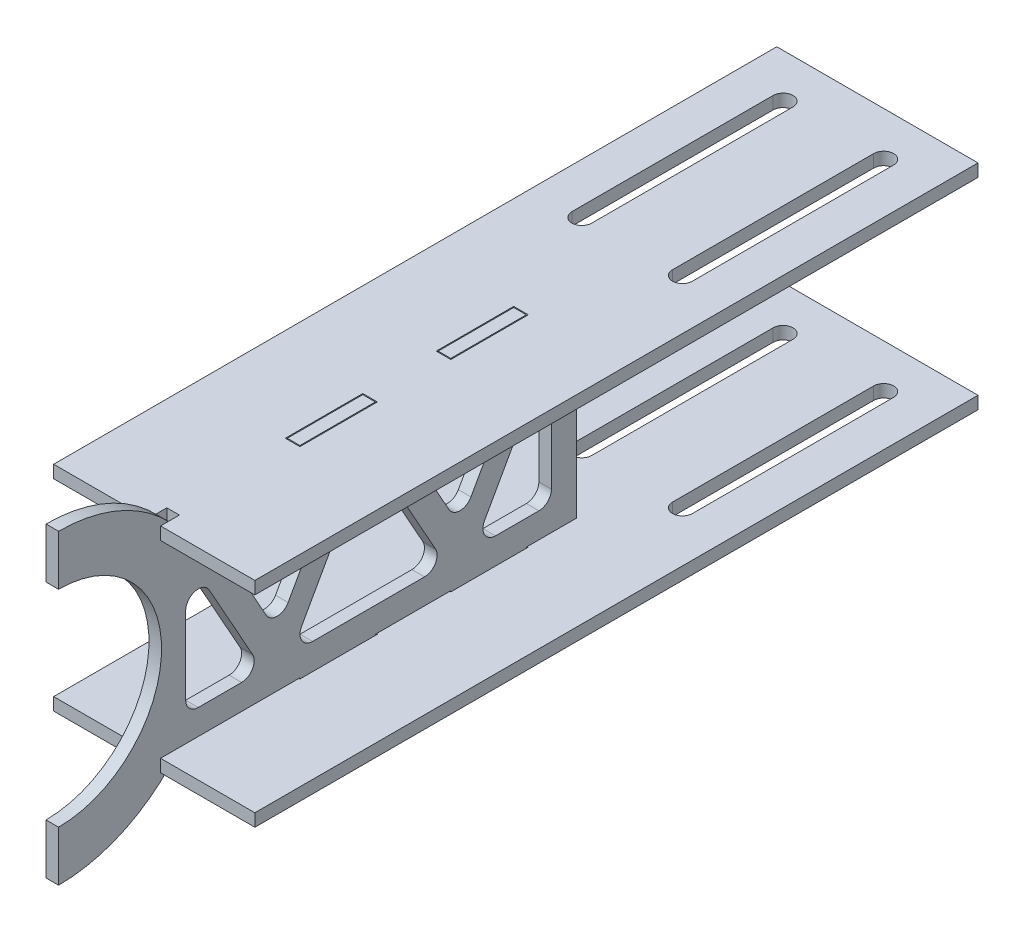
SolidWorks part; units mm, degrees
material "AISI 1020"
ref_plane "Front Plane" through (0, 0, 0) normal (0, 0, 1) x (1, 0, 0)
ref_plane "Top Plane" through (0, 0, 0) normal (0, 1, 0) x (1, 0, 0)
ref_plane "Right Plane" through (0, 0, 0) normal (1, 0, 0) x (0, 0, -1)
sketch "Sketch1" plane through (0, 0, 0) normal (1, 0, 0) x (0, 0, -1)
  line L0 (0, 0) -> (160.9375, 0) construction
  line L1 (30.5066, 23.8125) -> (60.925, 23.8125)
  line L2 (30.5066, -23.8125) -> (60.925, -23.8125)
  line L3 (130.775, 23.8125) -> (130.775, -23.8125)
  line L4 (0, 38.7) -> (0, 26)
  line L5 (137.125, 23.8125) -> (184.75, 23.8125) construction
  line L6 (137.125, 23.8125) -> (137.125, -23.8125) construction
  line L7 (137.125, -23.8125) -> (184.75, -23.8125) construction
  line L8 (184.75, 23.8125) -> (184.75, -23.8125) construction
  line L9 (137.125, 23.8125) -> (184.75, -23.8125) construction
  line L10 (137.125, -23.8125) -> (184.75, 23.8125) construction
  line L11 (0, -26) -> (0, -38.7)
  line L34 (60.925, 23.8125) -> (60.925, 26.9875)
  line L35 (60.925, 26.9875) -> (79.975, 26.9875)
  line L36 (79.975, 26.9875) -> (79.975, 23.8125)
  line L37 (99.025, 23.8125) -> (99.025, 26.9875)
  line L38 (99.025, 26.9875) -> (118.075, 26.9875)
  line L39 (118.075, 26.9875) -> (118.075, 23.8125)
  line L40 (118.075, 23.8125) -> (130.775, 23.8125)
  line L41 (79.975, 23.8125) -> (99.025, 23.8125)
  line L43 (79.975, -23.8125) -> (99.025, -23.8125)
  line L44 (118.075, -26.9875) -> (118.075, -23.8125)
  line L45 (99.025, -26.9875) -> (118.075, -26.9875)
  line L46 (99.025, -23.8125) -> (99.025, -26.9875)
  line L47 (79.975, -26.9875) -> (79.975, -23.8125)
  line L48 (60.925, -26.9875) -> (79.975, -26.9875)
  line L49 (60.925, -23.8125) -> (60.925, -26.9875)
  line L52 (118.075, -23.8125) -> (130.775, -23.8125)
  arc A0 (0, -26) -> (0, 26) centre (0, 0) ccw
  arc A1 (30.5066, 23.8125) -> (0, 38.7) centre (0, 0) ccw
  arc A2 (0, -38.7) -> (30.5066, -23.8125) centre (0, 0) ccw
  circle A6 centre (0, 0) radius 48.225 construction
  point P1 (48.225, 0)
  point P11 (130.775, 0)
  dimension "D1" = 52
  dimension "D6" = 12.7
  dimension "D7" = 12.7
  dimension "D10" = 9.525
  dimension "D2" = 12.7
  dimension "D3" = 47.625
  dimension "D4" = 47.625
  dimension "D5" = 6.35
  dimension "D17" = 19.05
  dimension "D18" = 3.175
  dimension "D19" = 19.05
extrude "Boss-Extrude1" add sketch "Sketch1" along normal mid plane 3.175
sketch "Sketch2" plane through (0, 23.8125, 0) normal (0, 1, 0) x (1, 0, 0)
  line L0 (-1.5875, 30.5066) -> (1.5875, 30.5066)
  line L1 (1.5875, 30.5066) -> (-1.5875, 30.5066) construction
  line L2 (1.5875, 30.5066) -> (1.5875, 25.7441)
  line L3 (1.5875, 25.7441) -> (25.4, 25.7441)
  line L4 (25.4, 25.7441) -> (25.4, 208.3066)
  line L5 (25.4, 208.3066) -> (-25.4, 208.3066)
  line L6 (0, 208.3066) -> (0, 30.5066) construction
  line L7 (-12.7, 197.1941) -> (-12.7, 146.3941) construction
  line L8 (-12.7, 159.0941) -> (12.7, 159.0941) construction
  line L9 (-12.7, 159.0941) -> (-12.7, 184.4941) construction
  line L10 (-12.7, 184.4941) -> (12.7, 184.4941) construction
  line L12 (-12.7, 159.0941) -> (12.7, 184.4941) construction
  line L13 (-12.7, 184.4941) -> (12.7, 159.0941) construction
  line L14 (-12.7, 171.7941) -> (0, 171.7941) construction
  line L17 (12.7, 146.3941) -> (12.7, 197.1941) construction
  line L20 (10.1917, 146.3941) -> (10.1917, 197.1941)
  line L23 (15.2083, 146.3941) -> (15.2083, 197.1941)
  line L26 (-1.5875, 30.5066) -> (-1.5875, 25.7441)
  line L27 (-1.5875, 25.7441) -> (-25.4, 25.7441)
  line L28 (-25.4, 25.7441) -> (-25.4, 208.3066)
  line L29 (-1.5875, 118.075) -> (-1.5875, 99.025) construction
  line L30 (-1.5875, 99.025) -> (1.5875, 99.025) construction
  line L31 (1.5875, 99.025) -> (1.5875, 118.075) construction
  line L32 (1.5875, 118.075) -> (-1.5875, 118.075) construction
  line L33 (-1.5875, 79.975) -> (-1.5875, 60.925) construction
  line L34 (-1.5875, 60.925) -> (1.5875, 60.925) construction
  line L35 (1.5875, 60.925) -> (1.5875, 79.975) construction
  line L36 (1.5875, 79.975) -> (-1.5875, 79.975) construction
  line L37 (-1.5875, 118.075) -> (-1.5875, 99.025) construction
  line L38 (-1.5875, 99.025) -> (1.5875, 99.025) construction
  line L39 (1.5875, 99.025) -> (1.5875, 118.075) construction
  line L40 (1.5875, 118.075) -> (-1.5875, 118.075) construction
  line L41 (-1.5875, 79.975) -> (-1.5875, 60.925) construction
  line L42 (-1.5875, 60.925) -> (1.5875, 60.925) construction
  line L43 (1.5875, 60.925) -> (1.5875, 79.975) construction
  line L44 (1.5875, 79.975) -> (-1.5875, 79.975) construction
  line L45 (12.7, 197.1941) -> (12.7, 146.3941) construction
  line L46 (-12.7, 146.3941) -> (-12.7, 197.1941) construction
  line L47 (-10.1917, 146.3941) -> (-10.1917, 197.1941)
  line L48 (-15.2083, 146.3941) -> (-15.2083, 197.1941)
  line L57 (-1.8415, 118.329) -> (-1.8415, 98.771)
  line L58 (-1.8415, 98.771) -> (1.8415, 98.771)
  line L59 (1.8415, 98.771) -> (1.8415, 118.329)
  line L60 (1.8415, 118.329) -> (-1.8415, 118.329)
  line L61 (-1.8415, 118.329) -> (-1.8415, 98.771)
  line L62 (-1.8415, 98.771) -> (1.8415, 98.771)
  line L63 (1.8415, 98.771) -> (1.8415, 118.329)
  line L64 (1.8415, 118.329) -> (-1.8415, 118.329)
  line L69 (-1.8415, 80.229) -> (-1.8415, 60.671)
  line L70 (-1.8415, 60.671) -> (1.8415, 60.671)
  line L71 (1.8415, 60.671) -> (1.8415, 80.229)
  line L72 (1.8415, 80.229) -> (-1.8415, 80.229)
  line L73 (-1.8415, 80.229) -> (-1.8415, 60.671)
  line L74 (-1.8415, 60.671) -> (1.8415, 60.671)
  line L75 (1.8415, 60.671) -> (1.8415, 80.229)
  line L76 (1.8415, 80.229) -> (-1.8415, 80.229)
  circle A0 centre (12.7, 159.0941) radius 2.5082 construction
  arc A1 (10.1917, 146.3941) -> (15.2083, 146.3941) centre (12.7, 146.3941) ccw
  arc A2 (15.2083, 197.1941) -> (10.1917, 197.1941) centre (12.7, 197.1941) ccw
  arc A3 (-10.1917, 146.3941) -> (-15.2083, 146.3941) centre (-12.7, 146.3941) cw
  arc A4 (-15.2083, 197.1941) -> (-10.1917, 197.1941) centre (-12.7, 197.1941) cw
  point P4 (0, 171.7941)
  point P8 (12.7, 171.7941)
  point P17 (12.7, 171.7941)
  point P26 (-12.7, 171.7941)
  point P31 (0, 0)
  point P32 (0, 0)
  dimension "D5" = 11.1125
  dimension "D6" = 5.0165
  dimension "D1" = 50.8
  dimension "D2" = 25.4
  dimension "D3" = 4.7625
  dimension "D4" = 25.4
  dimension "D9" = 120.65
  dimension "D7" = 0.254
  dimension "D8" = 0.254
extrude "Boss-Extrude2" add sketch "Sketch2" along normal blind 3.175 separate body contours L0 L2 L3 L4 L5 L28 L27 L26
mirror "Mirror3" about plane through (0, 0, 0) normal (0, 1, 0) of bodies 102
sketch "Sketch3" plane through (1.5875, 0, 0) normal (1, 0, 0) x (0, 0, -1)
  line L0 (25.7441, 26.9875) -> (25.7441, 23.8125) construction
  line L1 (25.7441, 23.8125) -> (130.775, 23.8125)
  line L2 (25.7441, 23.8125) -> (25.7441, -23.8125)
  line L3 (25.7441, -23.8125) -> (130.775, -23.8125)
  line L4 (130.775, 23.8125) -> (130.775, -23.8125)
  line L5 (60.925, 23.8125) -> (30.5066, 23.8125) construction
  line L6 (32.0941, -17.4625) -> (32.0941, 17.4625)
  line L7 (32.0941, 17.4625) -> (55.1769, -23.8125)
  line L8 (55.1769, -23.8125) -> (78.2596, 17.4625)
  line L9 (78.2596, 17.4625) -> (101.3423, -23.8125)
  line L10 (101.3423, -23.8125) -> (124.425, 17.4625)
  line L11 (124.425, 17.4625) -> (124.425, -23.8125)
  line L15 (32.0941, -17.4625) -> (51.6257, -17.4625)
  line L16 (39.3697, 17.4625) -> (55.1769, -10.8029)
  line L17 (55.1769, -10.8029) -> (70.984, 17.4625)
  line L18 (32.0941, 17.4625) -> (124.425, 17.4625)
  line L19 (37.6363, 20.5619) -> (55.1769, -10.8029) construction
  line L20 (55.1769, -10.8029) -> (72.7174, 20.5619) construction
  line L21 (58.728, -17.4625) -> (97.7911, -17.4625)
  line L22 (85.5351, 17.4625) -> (101.3423, -10.8029)
  line L23 (101.3423, -10.8029) -> (117.1495, 17.4625)
  line L24 (83.8018, 20.5619) -> (101.3423, -10.8029) construction
  line L25 (101.3423, -10.8029) -> (118.8828, 20.5619) construction
  line L26 (104.8935, -17.4625) -> (124.425, -17.4625)
  dimension "D1" = 6.35
  dimension "D2" = 6.35
  dimension "D4" = 6.35
  dimension "D3" = 6.35
  dimension "D5" = 6.35
  dimension "D6" = 6.35
extrude "Cut-Extrude1" cut sketch "Sketch3" against normal through all contours L6 L15 L7 | L18 L16 L17 | L8 L21 L9 | L22 L23 L18 | L10 L26 L11
fillet "Fillet1" radius 3.175 15 edges at (0, -17.4625, -124.425) (0, 17.4625, -124.425) (0, -17.4625, -104.8935) (0, 17.4625, -117.1495) (0, -10.8029, -101.3423) (0, 17.4625, -85.5351) (0, -17.4625, -97.7911) (0, -17.4625, -58.728) (0, 17.4625, -78.2596) (0, -10.8029, -55.1769) (0, 17.4625, -39.3697) (0, 17.4625, -70.984) (0, -17.4625, -32.0941) (0, -17.4625, -51.6257) (0, 17.4625, -32.0941)
